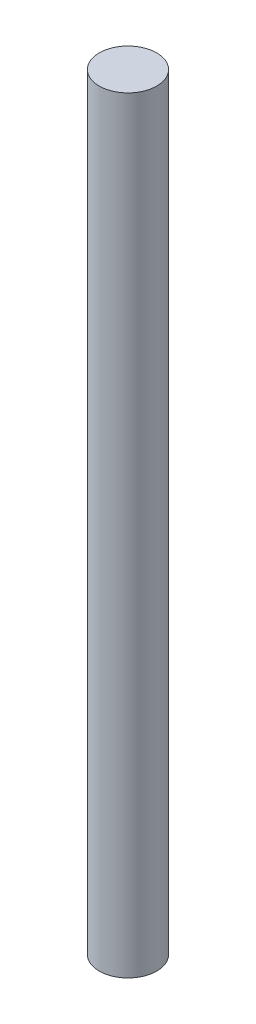
SolidWorks part; units mm, degrees
material "1060 Alloy"
ref_plane "Front Plane" through (0, 0, 0) normal (0, 0, 1) x (1, 0, 0)
ref_plane "Top Plane" through (0, 0, 0) normal (0, 1, 0) x (1, 0, 0)
ref_plane "Right Plane" through (0, 0, 0) normal (1, 0, 0) x (0, 0, -1)
sketch "Sketch1" plane through (0, 0, 0) normal (0, 1, 0) x (1, 0, 0)
  circle A0 centre (0, 0) radius 6
  dimension "D1" = 12
extrude "Boss-Extrude1" add sketch "Sketch1" along normal blind 160
